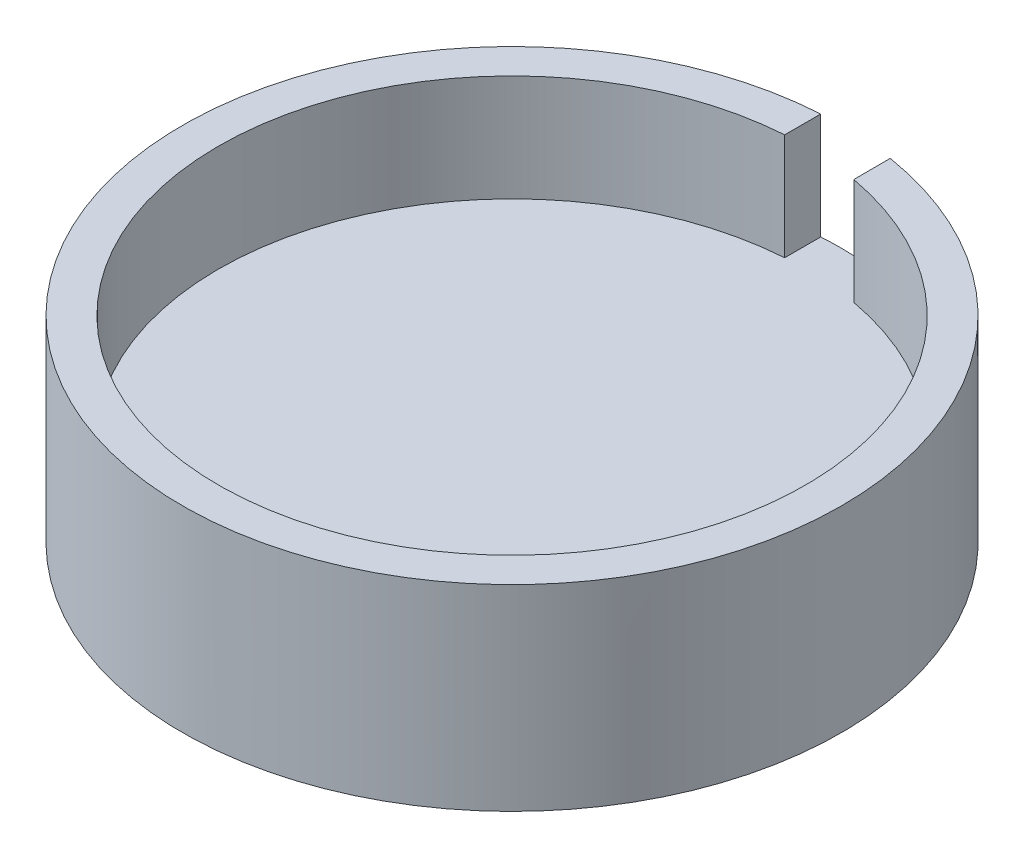
SolidWorks part; units mm, degrees
ref_plane "Front Plane" through (0, 0, 0) normal (0, 0, 1) x (1, 0, 0)
ref_plane "Top Plane" through (0, 0, 0) normal (0, 1, 0) x (1, 0, 0)
ref_plane "Right Plane" through (0, 0, 0) normal (1, 0, 0) x (0, 0, -1)
sketch "Sketch1" plane through (0, 0, 0) normal (0, 1, 0) x (1, 0, 0)
  circle A0 centre (0, 0) radius 58.166
  dimension "D1" = 116.332
extrude "Boss-Extrude1" add sketch "Sketch1" along normal blind 21.971 contours A0
sketch "Sketch3" plane through (0, 21.971, 0) normal (0, 1, 0) x (1, 0, 0)
  circle A0 centre (0, 0) radius 51.816
  dimension "D1" = 103.632
extrude "Cut-Extrude2" cut sketch "Sketch3" against normal blind 18.796
sketch "Sketch6" plane through (0, 21.971, 0) normal (0, 1, 0) x (1, 0, 0)
  line L0 (9.363, 50.963) -> (9.3408, 57.4111)
  line L1 (-3.5704, 51.6928) -> (-3.5704, 58.0563)
  arc A0 (9.3408, 57.4111) -> (-3.5704, 58.0563) centre (0, 0) ccw
  circle A1 centre (0, 0) radius 58.166 construction
  circle A2 centre (0, 0) radius 58.166 construction
  arc A3 (9.363, 50.963) -> (-3.5704, 51.6928) centre (0, 0) ccw
  circle A4 centre (0, 0) radius 51.816 construction
  circle A5 centre (0, 0) radius 51.816 construction
  dimension "D1" = 12.954
  dimension "D2" = 12.954
extrude "Cut-Extrude7" cut sketch "Sketch6" against normal blind 18.796
sketch "Sketch8" plane through (0, 0, 0) normal (0, -1, 0) x (1, 0, 0)
  circle A0 centre (0, 0) radius 58.166
extrude "Boss-Extrude4" add sketch "Sketch8" along normal blind 12.7
sketch "Sketch9" plane through (0, -12.7, 0) normal (0, -1, 0) x (1, 0, 0)
  circle A0 centre (-29.083, 0) radius 6.477
  circle A1 centre (29.083, 0) radius 6.477
  circle A2 centre (0, 0) radius 58.166 construction
  dimension "D1" = 12.954
  dimension "D2" = 12.954
  dimension "D3" = 29.083
  dimension "D4" = 29.083
extrude "Cut-Extrude8" cut sketch "Sketch9" against normal blind 12.7
